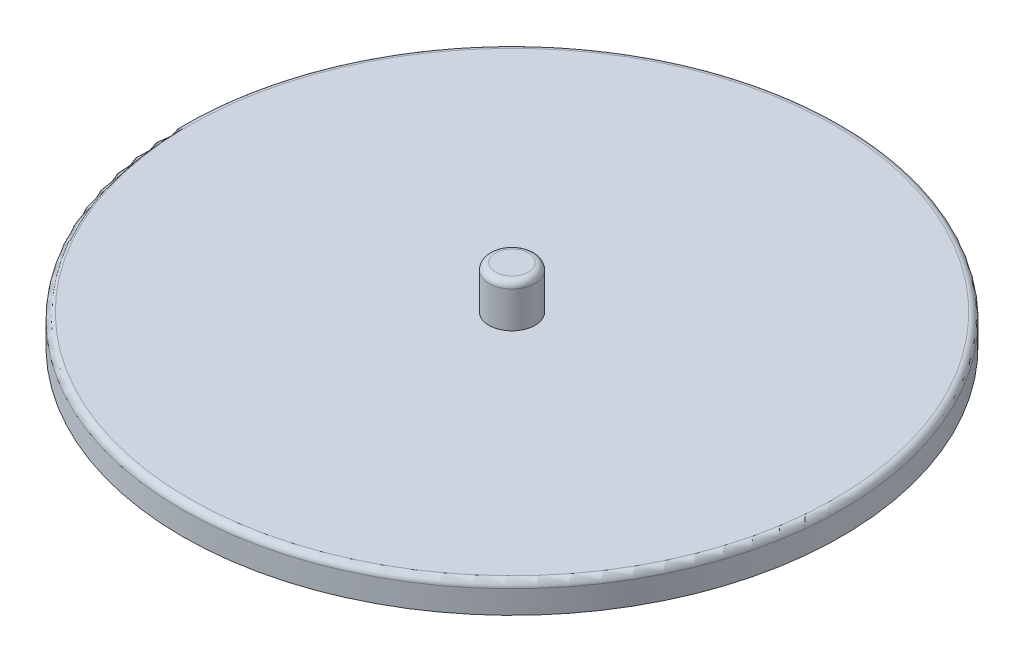
SolidWorks part; units mm, degrees
ref_plane "Front Plane" through (0, 0, 0) normal (0, 0, 1) x (1, 0, 0)
ref_plane "Top Plane" through (0, 0, 0) normal (0, 1, 0) x (1, 0, 0)
ref_plane "Right Plane" through (0, 0, 0) normal (1, 0, 0) x (0, 0, -1)
sketch "Sketch1" plane through (0, 0, 0) normal (0, 1, 0) x (1, 0, 0)
  circle A0 centre (0, 0) radius 100
  dimension "D1" = 200
extrude "Boss-Extrude1" add sketch "Sketch1" along normal blind 9 contours A0
sketch "Sketch2" plane through (0, 9, 0) normal (0, 1, 0) x (1, 0, 0)
  circle A0 centre (0, 0) radius 7
  dimension "D1" = 14
extrude "Boss-Extrude2" add sketch "Sketch2" along normal blind 13
fillet "Fillet1" radius 2 2 edges at (0, 22, 7) (0, 9, 100)
